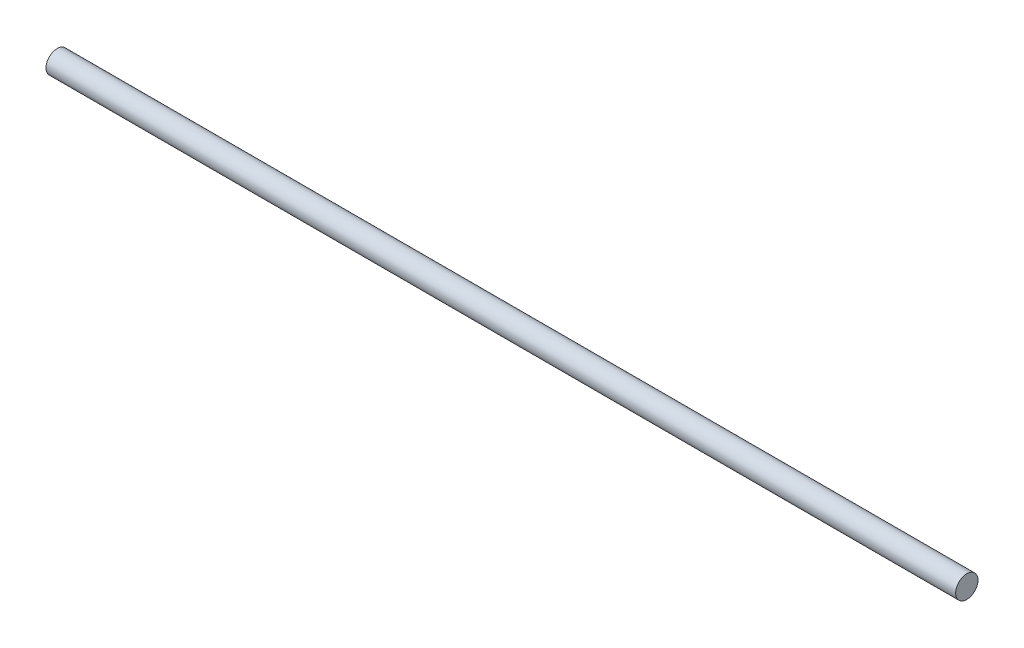
SolidWorks part; units mm, degrees
material "Plain Carbon Steel"
ref_plane "Front Plane" through (0, 0, 0) normal (0, 0, 1) x (1, 0, 0)
ref_plane "Top Plane" through (0, 0, 0) normal (0, 1, 0) x (1, 0, 0)
ref_plane "Right Plane" through (0, 0, 0) normal (1, 0, 0) x (0, 0, -1)
sketch "Sketch1" plane through (0, 0, 0) normal (1, 0, 0) x (0, 0, -1)
  circle A0 centre (0, 0) radius 0.75
  dimension "D1" = 1.5
extrude "Boss-Extrude1" add sketch "Sketch1" along normal blind 50 and the other way blind 11
